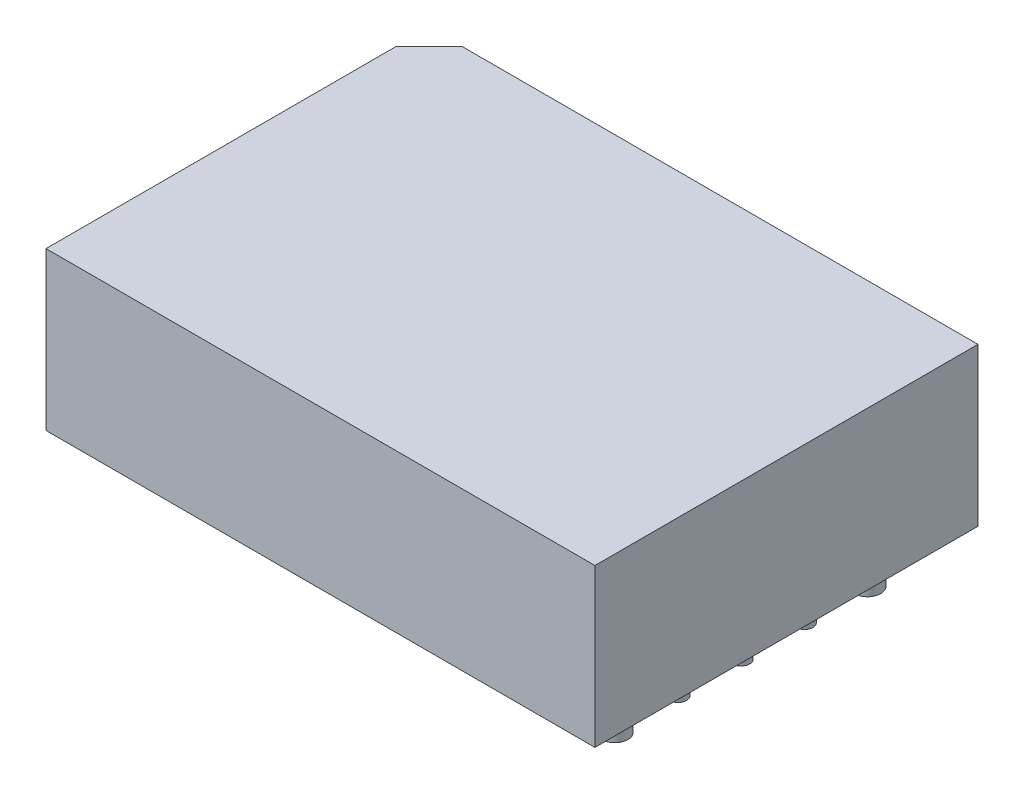
SolidWorks part; units mm, degrees
ref_plane "Front Plane" through (0, 0, 0) normal (0, 0, 1) x (1, 0, 0)
ref_plane "Top Plane" through (0, 0, 0) normal (0, 1, 0) x (1, 0, 0)
ref_plane "Right Plane" through (0, 0, 0) normal (1, 0, 0) x (0, 0, -1)
sketch "Sketch1" plane through (0, 0, 0) normal (0, 1, 0) x (1, 0, 0)
  line L0 (-31.1, 23.1) -> (-33.1, 21.1)
  line L1 (0, 0) -> (-33.1, 0)
  line L2 (0, 0) -> (0, 23.1)
  line L3 (0, 23.1) -> (-31.1, 23.1)
  line L4 (-33.1, 0) -> (-33.1, 21.1)
  point P1 (-33.1, 23.1)
  dimension "D1" = 33.1
  dimension "D2" = 23.1
extrude "Boss-Extrude1" add sketch "Sketch1" along normal blind 9.5
sketch "Sketch4" plane through (0, 9.5, 0) normal (0, 1, 0) x (1, 0, 0)
  line L0 (-33.1, 0) -> (0, 0) construction
  line L1 (0, 0) -> (0, 23.1) construction
  circle A0 centre (-30.64, 19.14) radius 0.51
  circle A1 centre (-30.64, 3.9) radius 0.51
  circle A2 centre (-2.7, 19.14) radius 0.51
  circle A3 centre (-2.7, 15.33) radius 0.51
  circle A4 centre (-2.7, 11.52) radius 0.51
  circle A5 centre (-2.7, 7.71) radius 0.51
  circle A6 centre (-2.7, 3.9) radius 0.51
  circle A7 centre (-2.7, 3.9) radius 0.785
  circle A8 centre (-2.7, 19.14) radius 0.785
  circle A9 centre (-30.64, 11.52) radius 0.51
  point P20 (0, 0)
  point P23 (0, 0)
  point P24 (0, 0)
  point P25 (0, 0)
  point P26 (0, 0)
  dimension "D2" = 1.02
  dimension "D3" = 1.57
  dimension "D1" = 27.94
  dimension "D4" = 3.9
  dimension "D5" = 3.81
  dimension "D6" = 7.62
  dimension "D7" = 11.43
  dimension "D8" = 15.24
  dimension "D9" = 2.7
extrude "Boss-Extrude2" add sketch "Sketch4" against normal blind 12 contours A2 | A8 A2 | A3 | A6 | A7 A6 | A5 | A4 | A1 | A0 | A9
